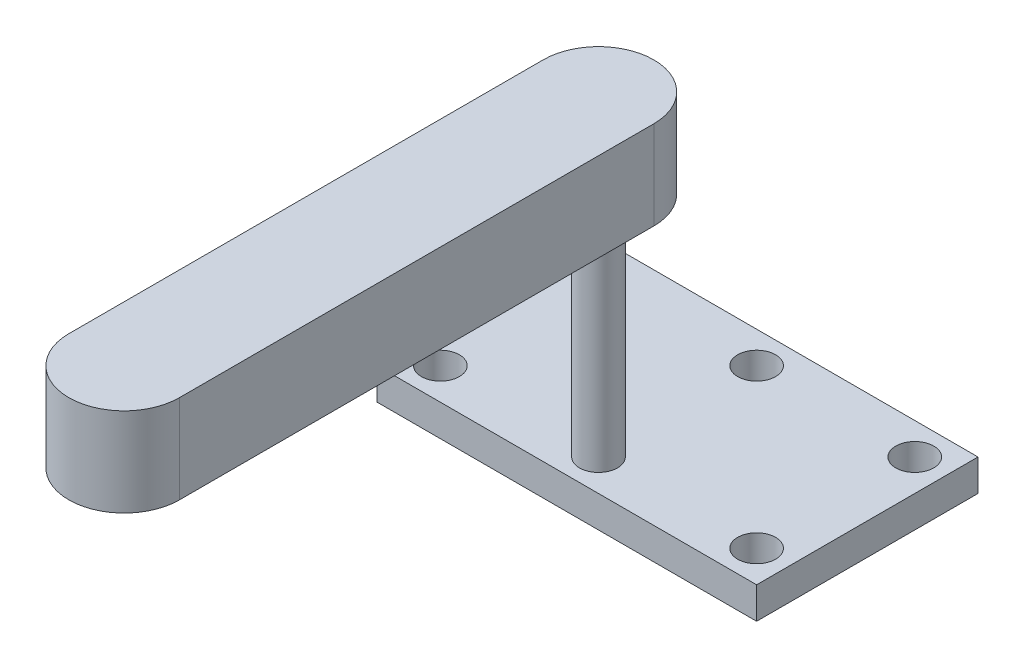
SolidWorks part; units mm, degrees
ref_plane "정면" through (0, 0, 0) normal (0, 0, 1) x (1, 0, 0)
ref_plane "윗면" through (0, 0, 0) normal (0, 1, 0) x (1, 0, 0)
ref_plane "우측면" through (0, 0, 0) normal (1, 0, 0) x (0, 0, -1)
sketch "스케치1" plane through (0, 0, 0) normal (0, 1, 0) x (1, 0, 0)
  line L1 (-30, 30) -> (30, 30)
  line L2 (-30, 30) -> (-30, -5)
  line L3 (-30, -5) -> (30, -5)
  line L4 (30, 30) -> (30, -5)
  circle A0 centre (0, 0) radius 3
  circle A1 centre (25, 0) radius 3
  circle A2 centre (-25, 0) radius 3
  circle A3 centre (25, 25) radius 3
  circle A4 centre (0, 25) radius 3
  circle A5 centre (-25, 25) radius 3
  dimension "D1" = 6
  dimension "D2" = 6
  dimension "D3" = 6
  dimension "D4" = 25
  dimension "D5" = 25
  dimension "D6" = 25
  dimension "D7" = 60
  dimension "D8" = 35
  dimension "D9" = 5
  dimension "D10" = 5
extrude "보스-돌출1" add sketch "스케치1" along normal blind 5
sketch "스케치2" plane through (0, 0, 0) normal (0, -1, 0) x (1, 0, 0)
  circle A0 centre (0, 0) radius 3
  dimension "D1" = 6
extrude "보스-돌출2" add sketch "스케치2" against normal blind 55
sketch "스케치3" plane through (0, 55, 0) normal (0, 1, 0) x (1, 0, 0)
  line L0 (0, 0) -> (0, -75) construction
  line L1 (8.75, 0) -> (8.75, -75)
  line L2 (-8.75, 0) -> (-8.75, -75)
  arc A0 (8.75, 0) -> (-8.75, 0) centre (0, 0) ccw
  arc A1 (-8.75, -75) -> (8.75, -75) centre (0, -75) ccw
  point P3 (0, -37.5)
  dimension "D1" = 17.5
  dimension "D2" = 75
extrude "보스-돌출3" add sketch "스케치3" against normal blind 14
